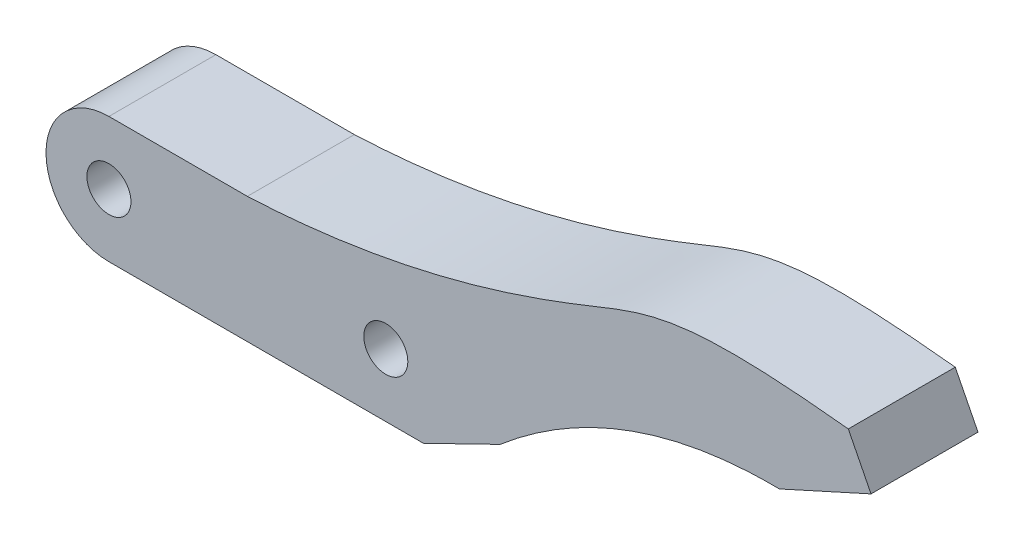
SolidWorks part; units mm, degrees
ref_plane "Front Plane" through (0, 0, 0) normal (0, 0, 1) x (1, 0, 0)
ref_plane "Top Plane" through (0, 0, 0) normal (0, 1, 0) x (1, 0, 0)
ref_plane "Right Plane" through (0, 0, 0) normal (1, 0, 0) x (0, 0, -1)
sketch "Sketch1" plane through (0, 0, 0) normal (0, 0, 1) x (1, 0, 0)
  line L1 (-5, 5) -> (27, 5)
  line L2 (-5, 5) -> (-5, -5)
  line L3 (-5, -5) -> (27, -5)
  line L4 (27, 5) -> (27, -5)
  circle A0 centre (0, 0) radius 5
  circle A1 centre (0, 0) radius 1.75
  circle A2 centre (22, 0) radius 1.75
  circle A3 centre (22, 0) radius 5
  dimension "D1" = 10
  dimension "D3" = 3.5
  dimension "D4" = 10
  dimension "D5" = 3.5
  dimension "D2" = 22
extrude "Boss-Extrude1" add sketch "Sketch1" along normal blind 8.5 contours A3 L1 A0 L3 | A3 A2 | A0 A1
sketch "Sketch2" plane through (0, 0, 8.5) normal (0, 0, 1) x (1, 0, 0)
  line L0 (22, -5) -> (24.99, -5)
  line L1 (24.99, -5) -> (31.08, -2.0297)
  line L2 (0, 5) -> (22, 5) construction
  line L3 (58.75, 12.87) -> (60.557, 9.3014)
  line L4 (60.557, 9.3014) -> (53.27, 6)
  line L5 (0, -5) -> (22, -5) construction
  line L8 (0, -5) -> (22, -5)
  line L9 (22, 5) -> (0, 5)
  line L11 (22, 5) -> (11, 5)
  arc A2 (22, -5) -> (22, 5) centre (22, 0) ccw
  arc A3 (0, 5) -> (0, -5) centre (0, 0) ccw
  arc A4 (22, -5) -> (22, 5) centre (22, 0) ccw
  spline S0 degree 3 poles (11, 5) (22.8337, 5.5232) (40.5808, 11.5038) (45.2455, 14.3222) (58.75, 12.87) knots 0 0 0 0 0.506899 1 1 1 1
  spline S1 degree 2 poles (31.08, -2.0297) (40.7387, 6.1883) (53.27, 6) knots 0 0 0 1 1 1
  dimension "D12" = 15.03
  dimension "D1" = 4
  dimension "D2" = 8
  dimension "D3" = 17.87
  dimension "D4" = 11
  dimension "D5" = 26
  dimension "D6" = 0
  dimension "D13" = 9.45
extrude "Boss-Extrude2" add sketch "Sketch2" against normal blind 8.5
